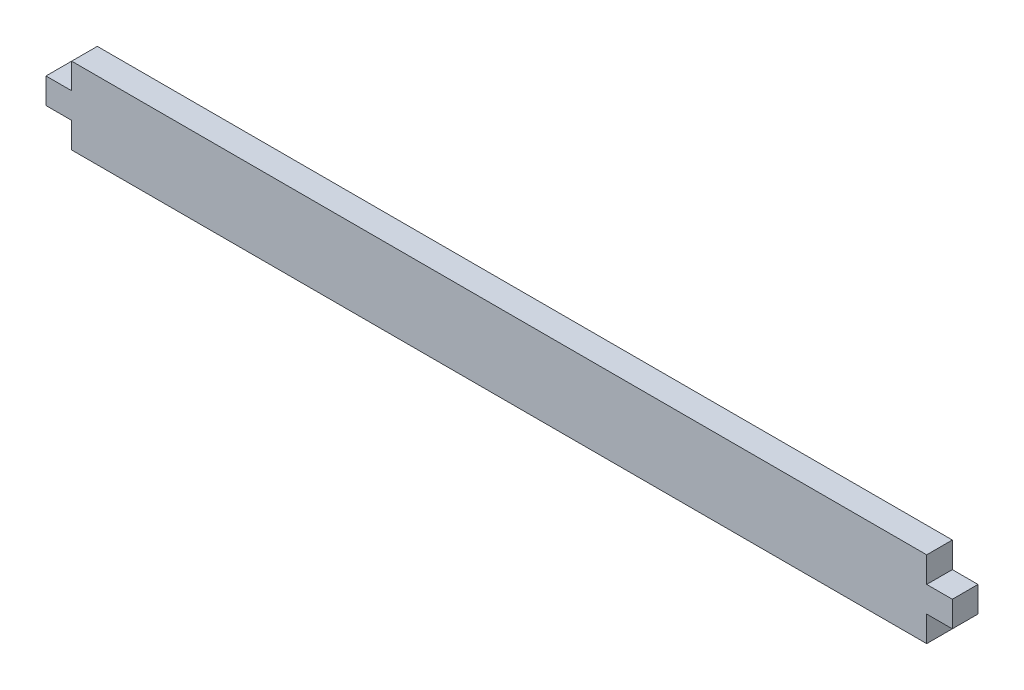
SolidWorks part; units mm, degrees
ref_plane "Alzado" through (0, 0, 0) normal (0, 0, 1) x (1, 0, 0)
ref_plane "Planta" through (0, 0, 0) normal (0, 1, 0) x (1, 0, 0)
ref_plane "Vista lateral" through (0, 0, 0) normal (1, 0, 0) x (0, 0, -1)
sketch "Croquis1" plane through (0, 0, 0) normal (0, 0, 1) x (1, 0, 0)
  line L0 (50, 9) -> (50, 0) construction
  line L1 (0, 0) -> (100, 0)
  line L2 (0, 0) -> (0, 3)
  line L3 (0, 9) -> (100, 9)
  line L4 (100, 0) -> (100, 3)
  line L5 (0, 6) -> (-3, 6)
  line L7 (0, 3) -> (-3, 3)
  line L8 (-3, 6) -> (-3, 3)
  line L9 (100, 3) -> (103, 3)
  line L10 (103, 6) -> (103, 3)
  line L11 (100, 6) -> (103, 6)
  line L13 (0, 6) -> (0, 9)
  line L14 (100, 6) -> (100, 9)
  dimension "D1" = 9
  dimension "D2" = 100
  dimension "D3" = 3
  dimension "D4" = 3
  dimension "D5" = 3
extrude "Saliente-Extruir1" add sketch "Croquis1" along normal blind 3
